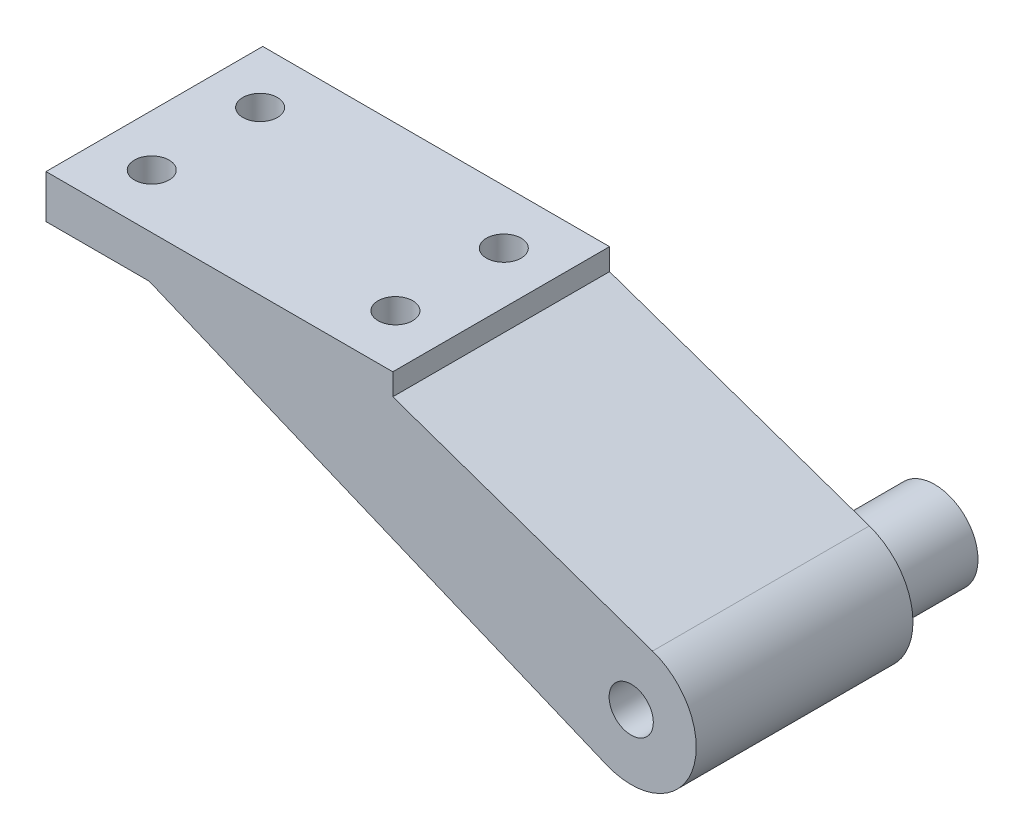
SolidWorks part; units mm, degrees
ref_plane "Front Plane" through (0, 0, 0) normal (0, 0, 1) x (1, 0, 0)
ref_plane "Top Plane" through (0, 0, 0) normal (0, 1, 0) x (1, 0, 0)
ref_plane "Right Plane" through (0, 0, 0) normal (1, 0, 0) x (0, 0, -1)
sketch "Sketch1" plane through (0, 0, 0) normal (0, 1, 0) x (1, 0, 0)
  line L1 (0, 0) -> (50.8, 0)
  line L2 (0, 0) -> (0, 31.75)
  line L3 (0, 31.75) -> (50.8, 31.75)
  line L4 (50.8, 0) -> (50.8, 31.75)
  dimension "D1" = 50.8
  dimension "D2" = 31.75
extrude "Boss-Extrude1" add sketch "Sketch1" along normal blind 6.35
sketch "Sketch2" plane through (0, 0, 0) normal (0, 0, 1) x (1, 0, 0)
  line L0 (0, 0) -> (50.8, 0) construction
  circle A1 centre (85.725, -19.05) radius 3.175 construction
  circle A2 centre (85.725, -19.05) radius 3.2385
  circle A3 centre (85.725, -19.05) radius 9.525
  circle A4 centre (85.725, -19.05) radius 3.2385 construction
  dimension "D1" = 6.477
  dimension "D2" = 19.05
  dimension "D3" = 85.725
  dimension "D4" = 19.05
extrude "Boss-Extrude2" add sketch "Sketch2" against normal up to surface (31.75 mm away) separate body up to face at (25.4, 3.175, -31.75)
sketch "Sketch3" plane through (0, 0, 0) normal (0, 0, 1) x (1, 0, 0)
  line L0 (50.8, 3.175) -> (88.8526, -10.0531)
  line L1 (50.8, 6.35) -> (50.8, 0) construction
  line L2 (82.0678, -27.8449) -> (15.105, 0)
  line L3 (0, 0) -> (50.8, 0) construction
  line L4 (15.105, 0) -> (15.105, 3.175)
  line L5 (15.105, 3.175) -> (50.8, 3.175)
  circle A1 centre (85.725, -19.05) radius 9.525 construction
  arc A2 (88.8526, -10.0531) -> (82.0678, -27.8449) centre (85.725, -19.05) ccw
extrude "Boss-Extrude3" add sketch "Sketch3" against normal up to surface (31.75 mm away) up to face at (25.4, 3.175, -31.75)
sketch "Sketch4" plane through (0, 0, -31.75) normal (0, 0, 1) x (1, 0, 0)
  circle A0 centre (85.725, -19.05) radius 3.2385
  circle A1 centre (85.725, -19.05) radius 6.35
sketch "Sketch5" plane through (0, 0, 0) normal (0, -1, 0) x (1, 0, 0)
  line L0 (7.5525, 0) -> (7.5525, -7.9375) construction
  line L1 (0, 0) -> (15.105, 0) construction
  line L2 (7.5525, -7.9375) -> (7.5525, -15.875) construction
  line L3 (7.5525, -15.875) -> (7.5525, -23.8125) construction
  line L4 (7.5525, -23.8125) -> (7.5525, -31.75) construction
  line L5 (15.105, -31.75) -> (0, -31.75) construction
  circle A0 centre (7.5525, -7.9375) radius 2.54
  circle A1 centre (7.5525, -23.8125) radius 2.54
  dimension "D1" = 5.08
extrude "Cut-Extrude1" cut sketch "Sketch5" against normal up to next
sketch "Sketch6" plane through (0, 6.35, 0) normal (0, 1, 0) x (1, 0, 0)
  line L0 (7.5525, 7.9375) -> (0, 7.9375) construction
  line L1 (0, 31.75) -> (0, 0) construction
  line L2 (50.8, 7.9375) -> (43.2475, 7.9375) construction
  line L3 (50.8, 0) -> (50.8, 31.75) construction
  line L4 (7.5525, 23.8125) -> (43.2475, 23.8125) construction
  line L5 (43.2475, 23.8125) -> (43.2475, 7.9375) construction
  circle A0 centre (43.2475, 7.9375) radius 2.54
  circle A1 centre (43.2475, 23.8125) radius 2.54
  circle A2 centre (7.5525, 7.9375) radius 2.54 construction
extrude "Cut-Extrude2" cut sketch "Sketch6" against normal through all
ref_plane "Plane9" through (0, -19.05, 0) normal (0, 1, 0) x (1, 0, 0)
sketch "Sketch7" plane through (0, -19.05, 0) normal (0, 1, 0) x (1, 0, 0)
  circle A0 centre (43.2475, 7.9375) radius 2.54 construction
  circle A1 centre (43.2475, 23.8125) radius 2.54 construction
  circle A2 centre (43.2475, 7.9375) radius 2.54 construction
  circle A3 centre (43.2475, 23.8125) radius 2.54 construction
  circle A4 centre (43.2475, 23.8125) radius 4.7625
  circle A5 centre (43.2475, 7.9375) radius 4.7625
  dimension "D1" = 9.525
extrude "Cut-Extrude3" cut sketch "Sketch7" along normal up to surface (19.05 mm away) up to face at (7.5525, 0, -26.3525)
extrude "Boss-Extrude4" add sketch "Sketch4" against normal blind 12.7
